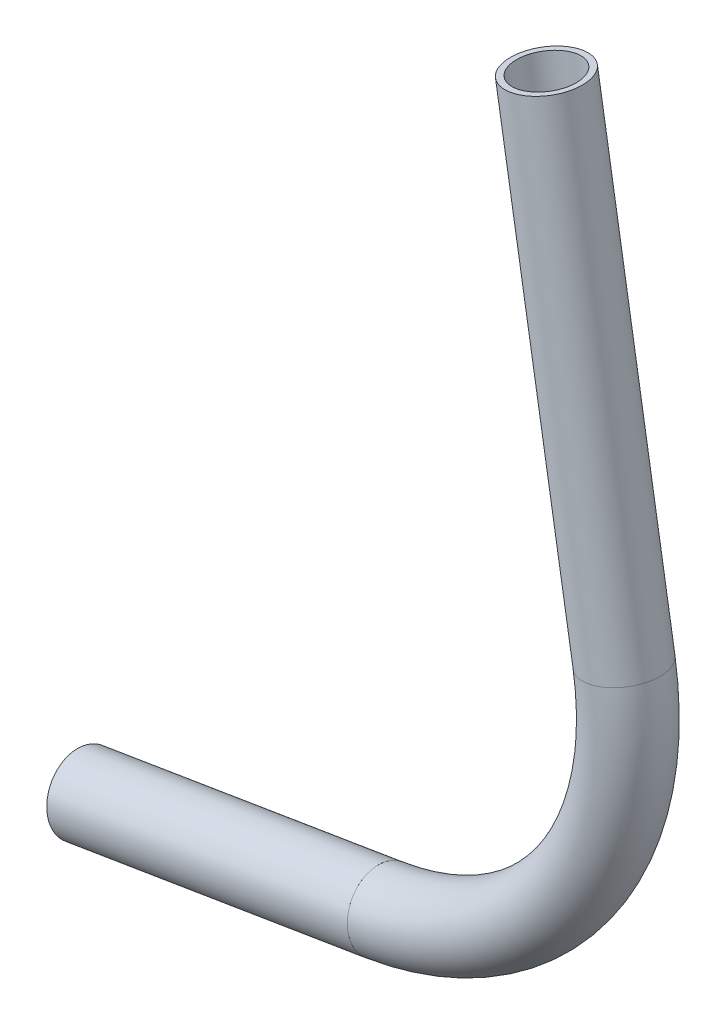
SolidWorks part; units mm, degrees
ref_plane "Front Plane" through (0, 0, 0) normal (0, 0, 1) x (1, 0, 0)
ref_plane "Top Plane" through (0, 0, 0) normal (0, 1, 0) x (1, 0, 0)
ref_plane "Right Plane" through (0, 0, 0) normal (1, 0, 0) x (0, 0, -1)
sketch "Sketch1" plane through (0, 0, 0) normal (0, 0, 1) x (1, 0, 0)
  line L0 (99.6262, 633.2007) -> (152.1193, 641.8088)
  line L2 (194.0291, 700.1599) -> (180.471, 782.8385)
  arc A0 (152.1193, 641.8088) -> (194.0291, 700.1599) centre (143.8986, 691.9392) ccw
  dimension "D1" = 50.8
other "Pipe 0.5 SCH 40(1)"
ref_plane "Plane1" through (99.6262, 633.2007, 0) normal (0.9868, 0.1618, 0) x (-0.1618, 0.9868, 0)
sketch "Sketch11" plane through (99.6262, 633.2007, 0) normal (0.9868, 0.1618, 0) x (-0.1618, 0.9868, 0)
  circle A0 centre (0, 0) radius 5.2832
  circle A1 centre (0, 0) radius 6.35
  point P5 (0, 0)
  dimension "In_dia" = 10.5664
  dimension "Out_dia" = 12.7
